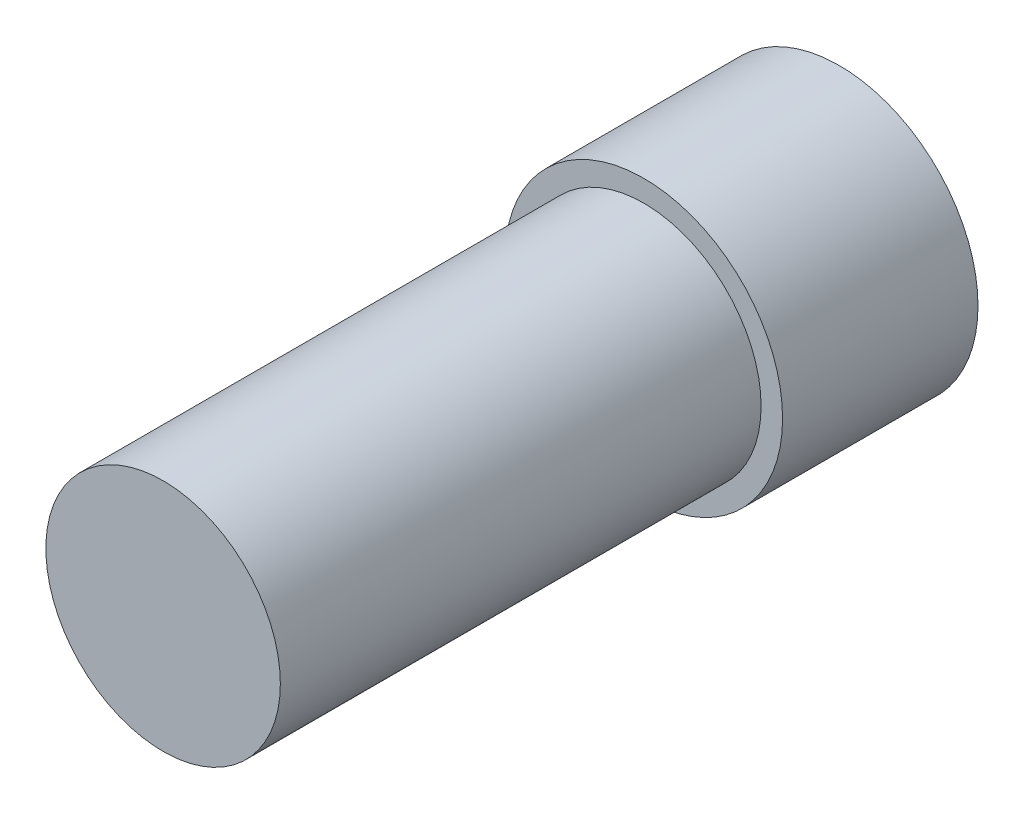
SolidWorks part; units mm, degrees
ref_plane "Front Plane" through (0, 0, 0) normal (0, 0, 1) x (1, 0, 0)
ref_plane "Top Plane" through (0, 0, 0) normal (0, 1, 0) x (1, 0, 0)
ref_plane "Right Plane" through (0, 0, 0) normal (1, 0, 0) x (0, 0, -1)
sketch "Sketch1" plane through (0, 0, 0) normal (0, 0, 1) x (1, 0, 0)
  circle A0 centre (0, 0) radius 7.1
  circle A1 centre (0, 0) radius 3
  dimension "D1" = 14.2
  dimension "D2" = 6
extrude "Boss-Extrude1" add sketch "Sketch1" along normal blind 10
sketch "Sketch2" plane through (0, 0, 10) normal (0, 0, 1) x (1, 0, 0)
  circle A0 centre (0, 0) radius 6
  circle A1 centre (0, 0) radius 3
  dimension "D1" = 12
extrude "Boss-Extrude2" add sketch "Sketch2" along normal up to surface (24.6 mm away) contours A0
